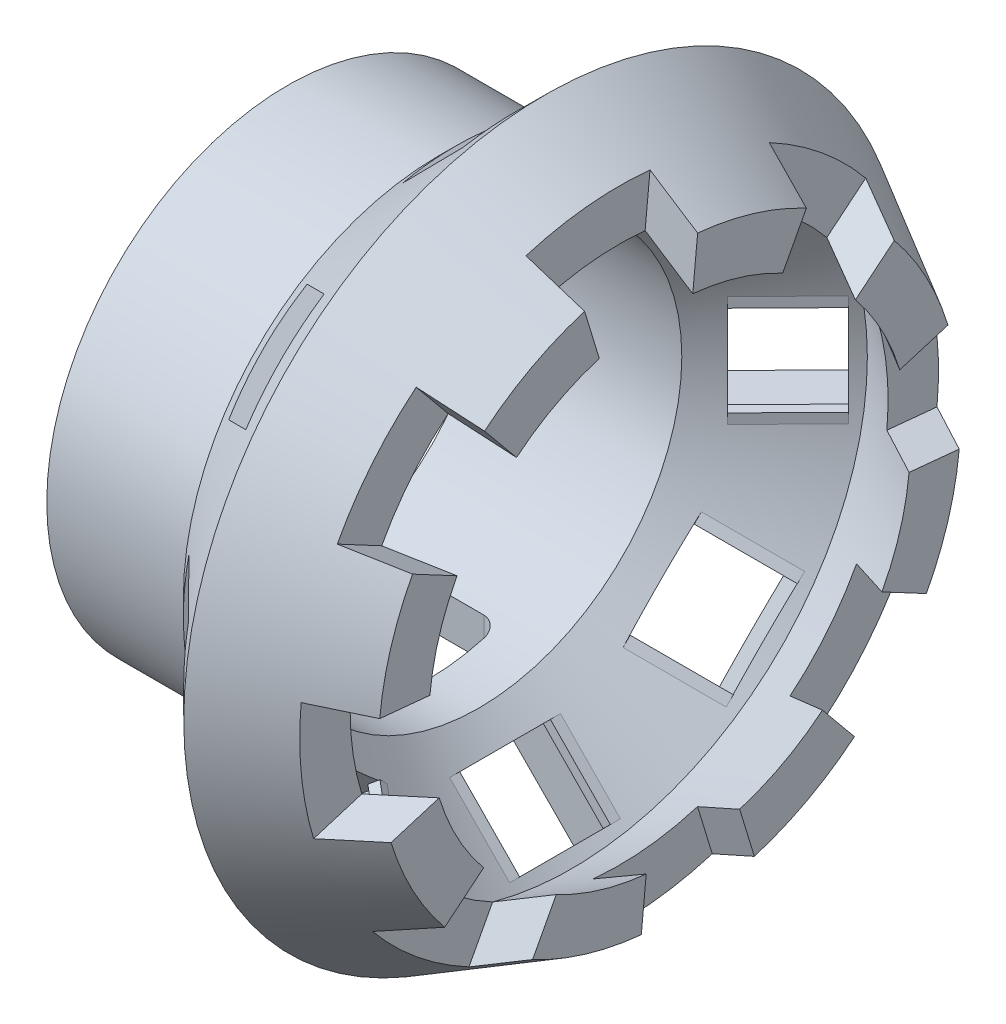
SolidWorks part; units mm, degrees
other "标注1"
sketch "草图8" plane through (-2.7147, -6.8585, 6.8585) normal (-0.2235, -0.0225, 0.9745) x (-0.1799, 0.9835, -0.0185)
ref_plane "前视基准面" through (0, 0, 0) normal (0, 0, 1) x (1, 0, 0)
ref_plane "上视基准面" through (0, 0, 0) normal (0, 1, 0) x (1, 0, 0)
ref_plane "右视基准面" through (0, 0, 0) normal (1, 0, 0) x (0, 0, -1)
sketch "草图1" plane through (0, 0, 0) normal (0, 0, 1) x (1, 0, 0)
  line L7 (8.0647, 7.1695) -> (11.04, 5.5)
  line L8 (11.04, 5.5) -> (11.04, 4.5)
  line L9 (11.04, 4.5) -> (8.6008, 5.8686)
  line L11 (7.54, 5.8) -> (7.54, 0) construction
  line L12 (0, 0) -> (8.3011, 0) construction
  line L13 (8.034, 5.3041) -> (7.54, 5.8) construction
  line L14 (6.755, 4.03) -> (8.6008, 5.8686)
  line L16 (11.04, 4.5) -> (11.04, -0.8919) construction
  line L17 (8.034, 5.3041) -> (11.109, 2.217) construction
  line L23 (5.955, 5.068) -> (8.0647, 7.1695)
  line L24 (6.0503, 4.03) -> (7.3502, 4.03) construction
  line L25 (5.955, 5.068) -> (5.955, 4.78)
  line L28 (6.0503, 4.03) -> (6.755, 4.03)
  line L31 (6.0503, 4.03) -> (2.955, 4.03)
  line L33 (5.955, 4.78) -> (2.955, 4.78)
  line L34 (2.955, 4.03) -> (2.955, 4.78)
  point P5 (8.035, 7.1932)
  dimension "D1" = 4.5
  dimension "D2" = 3
  dimension "D3" = 0.8
  dimension "D4" = 4.03
  dimension "D5" = 0.8
  dimension "D6" = 0.7
  dimension "D7" = 5.8
  dimension "D8" = 1.3
  dimension "D9" = 1
  dimension "D10" = 3.5
  dimension "D13" = 0.75
revolve "旋转1" add sketch "草图1" angle 360 about L12
sketch "草图2" plane through (0, 0, 0) normal (0, 1, 0) x (1, 0, 0)
  line L1 (3.0145, -5.257) -> (4.0717, -5.257) construction
  line L8 (5.955, -5.068) -> (8.0647, -7.1695) construction
  line L9 (5.1803, -6.5082) -> (7.3988, -4.2897)
  line L10 (5.1803, -6.5082) -> (6.3824, -7.7103)
  line L11 (6.3824, -7.7103) -> (8.6009, -5.4918)
  line L12 (7.3988, -4.2897) -> (8.6009, -5.4918)
  line L13 (5.1803, -6.5082) -> (8.6009, -5.4918) construction
  line L14 (6.3824, -7.7103) -> (7.3988, -4.2897) construction
  line L15 (0, 0) -> (-4.3641, 0) construction
  line L16 (6.8906, -6) -> (5.7814, -7.1092) construction
  line L17 (5.955, -5.068) -> (8.0647, -7.1695) construction
  line L18 (5.955, -5.068) -> (8.0647, -7.1695) construction
  line L19 (5.955, -5.068) -> (8.0647, -7.1695) construction
  dimension "D1" = 45
  dimension "D2" = 1.7
  dimension "D3" = 6
extrude "切除-拉伸1" cut sketch "草图2" against normal mid plane 2.2
sketch "草图3" plane through (0, 0, 0) normal (0, 1, 0) x (1, 0, 0)
  line L0 (0, 0) -> (-2.7147, 0) construction
pattern_circular "阵列(圆周)1" count 8 over 360 about axis through (0, 0, 0) along (1, 0, 0) of "切除-拉伸1"
ref_plane "基准面2" through (1.5037, 0, -1.4741) normal (0.7141, 0, -0.7001) x (-0.7001, 0, -0.7141)
sketch "草图5" plane through (1.5037, 0, -1.4741) normal (0.7141, 0, -0.7001) x (-0.7001, 0, -0.7141)
  line L0 (-9.9446, 1.1) -> (-8.2445, 1.1)
  line L1 (-9.9446, 1.1) -> (-9.9446, 0.9)
  line L2 (-8.2445, 1.1) -> (-8.2445, 0.9)
  line L3 (-9.9446, 0.9) -> (-8.2445, 0.9)
  line L4 (-9.9446, -1.1) -> (-8.2445, -1.1)
  line L5 (-9.9446, -1.1) -> (-9.9446, -0.9)
  line L6 (-8.2445, -1.1) -> (-8.2445, -0.9)
  line L7 (-9.9446, -0.9) -> (-8.2445, -0.9)
  dimension "D1" = 0.2
  dimension "D2" = 0.2
extrude "凸台-拉伸1" add sketch "草图5" against normal blind 0.2
sketch "草图6" plane through (0, 0, 0) normal (0, 0, 1) x (1, 0, 0)
  line L0 (5.955, 5.068) -> (5.955, -5.068) construction
  line L1 (-2.939, 5.7136) -> (2.955, 5.7136)
  line L2 (-2.939, 5.7136) -> (-2.939, -5.5135)
  line L3 (-2.939, -5.5135) -> (2.955, -5.5135)
  line L4 (2.955, 5.7136) -> (2.955, -5.5135)
  line L5 (10.54, 7.4147) -> (14.0576, 7.4147)
  line L6 (10.54, 7.4147) -> (10.54, -7.7149)
  line L7 (10.54, -7.7149) -> (14.0576, -7.7149)
  line L8 (14.0576, 7.4147) -> (14.0576, -7.7149)
  line L9 (11.04, -5.5) -> (11.04, 5.5) construction
  dimension "D1" = 3
  dimension "D2" = 0.5
extrude "切除-拉伸2" cut sketch "草图6" against normal mid plane 20
ref_plane "基准面3" through (1.5037, -1.4741, 0) normal (-0.7141, 0.7001, 0) x (0, 0, 1)
sketch "草图7" plane through (1.5037, -1.4741, 0) normal (-0.7141, 0.7001, 0) x (0, 0, 1)
  line L0 (1.1, 9.9446) -> (1.1, 8.2445)
  line L1 (1.1, 9.9446) -> (0.9, 9.9446)
  line L2 (1.1, 8.2445) -> (0.9, 8.2445)
  line L3 (0.9, 9.9446) -> (0.9, 8.2445)
  line L4 (-1.1, 8.2445) -> (-1.1, 9.9446)
  line L5 (-1.1, 8.2445) -> (-0.9, 8.2445)
  line L6 (-1.1, 9.9446) -> (-0.9, 9.9446)
  line L7 (-0.9, 8.2445) -> (-0.9, 9.9446)
  dimension "D1" = 0.2
  dimension "D2" = 0.2
extrude "凸台-拉伸2" add sketch "草图7" along normal blind 0.2
pattern_circular "阵列(圆周)2" count 8 over 360 about axis through (0, 0, 0) along (1, 0, 0) of "凸台-拉伸2"
sketch "草图9" plane through (10.54, 0, 0) normal (1, 0, 0) x (0, 0, -1)
  line L2 (0, 0) -> (-2.1978, 7.2108)
  line L3 (0, 0) -> (0.729, 7.503)
  line L4 (0, 0) -> (3.5447, 6.6529)
  line L5 (0, 0) -> (5.8208, 4.7899)
  line L6 (0, 0) -> (7.2108, 2.1978)
  line L7 (0, 0) -> (7.503, -0.729)
  line L8 (0, 0) -> (6.6529, -3.5447)
  line L9 (0, 0) -> (4.7899, -5.8208)
  line L10 (0, 0) -> (2.1978, -7.2108)
  line L11 (0, 0) -> (-0.729, -7.503)
  line L12 (0, 0) -> (-3.5447, -6.6529)
  line L13 (0, 0) -> (-5.8208, -4.7899)
  line L14 (0, 0) -> (-7.2108, -2.1978)
  line L15 (0, 0) -> (-7.503, 0.729)
  line L16 (0, 0) -> (-6.6529, 3.5447)
  line L17 (0, 0) -> (-4.7899, 5.8208)
  arc A2 (-2.1978, 7.2108) -> (0.729, 7.503) centre (0, 0) cw
  arc A4 (3.5447, 6.6529) -> (5.8208, 4.7899) centre (0, 0) cw
  arc A5 (7.2108, 2.1978) -> (7.503, -0.729) centre (0, 0) cw
  arc A6 (6.6529, -3.5447) -> (4.7899, -5.8208) centre (0, 0) cw
  arc A7 (2.1978, -7.2108) -> (-0.729, -7.503) centre (0, 0) cw
  arc A8 (-3.5447, -6.6529) -> (-5.8208, -4.7899) centre (0, 0) cw
  arc A9 (-7.2108, -2.1978) -> (-7.503, 0.729) centre (0, 0) cw
  arc A10 (-6.6529, 3.5447) -> (-4.7899, 5.8208) centre (0, 0) cw
  point P21 (0, 0)
  circle M4 centre (0, 0) radius 5.7805
  circle M5 centre (0, 0) radius 4.7805
  dimension "D1" = 22.5
  dimension "D2" = 8
extrude "切除-拉伸3" cut sketch "草图9" against normal blind 1 contours L8 L9 M5 | L9 L8 M5 M4 | A6 L8 L9 M4 | A7 L10 L11 M4 | L11 L10 M5 M4 | L10 L11 M5 | A8 L12 L13 M4 | L13 L12 M5 M4 | L12 L13 M5 | A9 L14 L15 M4 | L15 L14 M5 M4 | L14 L15 M5 | A10 L16 L17 M4 | L17 L16 M5 M4 | L16 L17 M5 | L2 L3 M5 | L3 L2 M5 M4 | A2 L2 L3 M4 | A4 L4 L5 M4 | L5 L4 M5 M4 | L4 L5 M5 | A5 L6 L7 M4 | L7 L6 M5 M4 | L6 L7 M5
sketch "草图10" plane through (2.955, 0, 0) normal (-1, 0, 0) x (0, 0, 1)
  line L0 (0, 0) -> (0, -3.1283) construction
  line L1 (-1.4, -0.9467) -> (1.4, -0.9467)
  line L2 (-1.4, -0.9467) -> (-1.4, -5.3098)
  line L3 (-1.4, -5.3098) -> (1.4, -5.3098)
  line L4 (1.4, -0.9467) -> (1.4, -5.3098)
  line L5 (-1.4, -0.9467) -> (1.4, -5.3098) construction
  line L6 (-1.4, -5.3098) -> (1.4, -0.9467) construction
  point P0 (0, -3.1283)
  dimension "D1" = 2.8
extrude "切除-拉伸4" cut sketch "草图10" against normal offset from surface (2.8 mm away) 0.2 up to face at (5.955, 0, 4.78)
fillet "圆角1" radius 0.3 4 edges at (5.755, -4.1747, 1.4) (5.755, -4.1747, -1.4) (2.955, -4.1747, 1.4) (2.955, -4.1747, -1.4)
